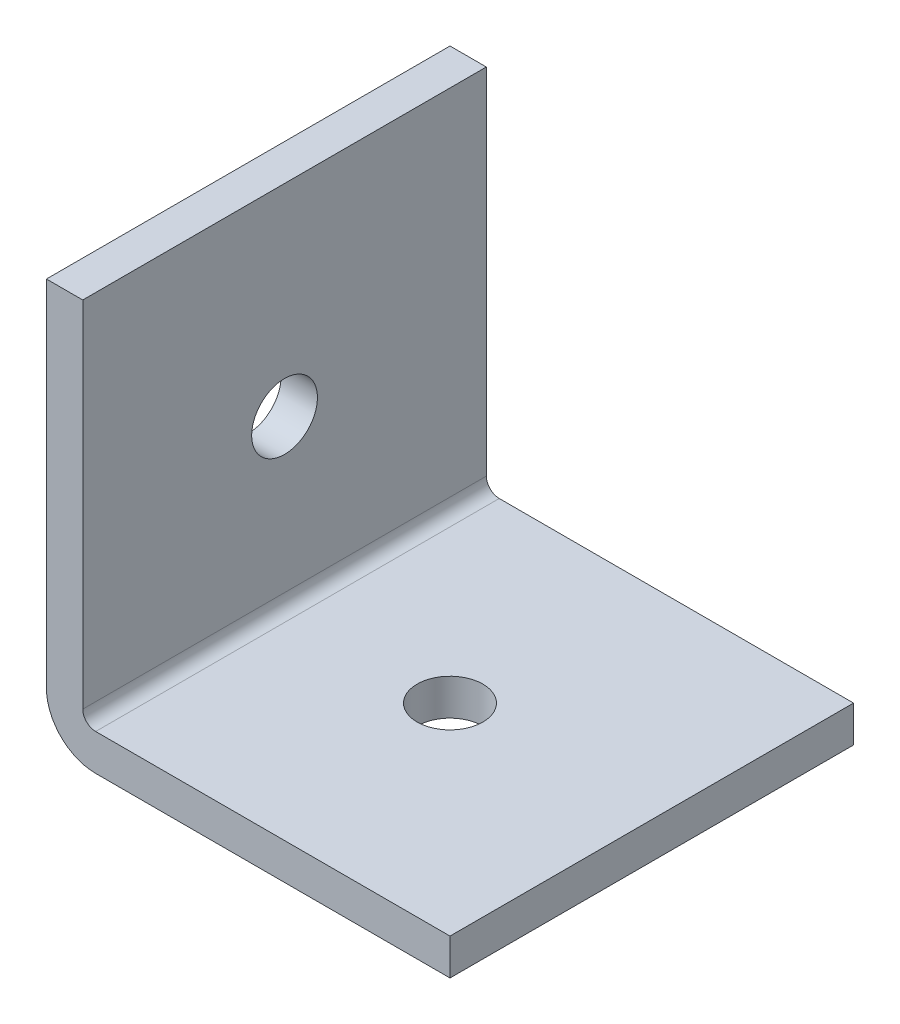
SolidWorks part; units mm, degrees
material "6061-T6 (SS)"
ref_plane "Front Plane" through (0, 0, 0) normal (0, 0, 1) x (1, 0, 0)
ref_plane "Top Plane" through (0, 0, 0) normal (0, 1, 0) x (1, 0, 0)
ref_plane "Right Plane" through (0, 0, 0) normal (1, 0, 0) x (0, 0, -1)
ref_plane "Plane1" through (0, 0, 0) normal (-1, 0, 0) x (0, -1, 0)
sketch "Sketch1" plane through (0, 0, 0) normal (-1, 0, 0) x (0, -1, 0)
  line L0 (0, 749.3) -> (-25.4, 749.3)
  line L1 (-25.4, 749.3) -> (-25.4, -749.3)
  line L2 (-25.4, -749.3) -> (0, -749.3)
  line L3 (0, -749.3) -> (0, 749.3)
extrude "Boss-Extrude1" add sketch "Sketch1" against normal blind 25.4
sketch "Sketch2" plane through (0, 0, -749.3) normal (0, 0, -1) x (-1, 0, 0)
  line L0 (-25.4, 2.286) -> (-2.286, 2.286)
  line L1 (-2.286, 2.286) -> (-2.286, 25.4)
  line L2 (-2.286, 25.4) -> (-25.4, 25.4)
  line L3 (-25.4, 25.4) -> (-25.4, 2.286)
extrude "Cut-Extrude1" cut sketch "Sketch2" against normal through all
hole_wizard "M3.5 Clearance Hole1" positions "Sketch4" profile "Sketch3" hole size "M3.5" standard "ANSI Metric"
sketch "Sketch4" plane through (0, 0, 0) normal (0, -1, 0) x (-1, 0, 0)
  point P0 (-12.7, 736.6)
  point P1 (-12.7, 711.2)
  point P2 (-12.7, 685.8)
  point P3 (-12.7, 660.4)
  point P4 (-12.7, 635)
  point P5 (-12.7, 609.6)
  point P6 (-12.7, 584.2)
  point P7 (-12.7, 558.8)
  point P8 (-12.7, 533.4)
  point P9 (-12.7, 508)
  point P10 (-12.7, 482.6)
  point P11 (-12.7, 457.2)
  point P12 (-12.7, 431.8)
  point P13 (-12.7, 406.4)
  point P14 (-12.7, 381)
  point P15 (-12.7, 355.6)
  point P16 (-12.7, 330.2)
  point P17 (-12.7, 304.8)
  point P18 (-12.7, 279.4)
  point P19 (-12.7, 254)
  point P20 (-12.7, 228.6)
  point P21 (-12.7, 203.2)
  point P22 (-12.7, 177.8)
  point P23 (-12.7, 152.4)
  point P24 (-12.7, 127)
  point P25 (-12.7, 101.6)
  point P26 (-12.7, 76.2)
  point P27 (-12.7, 50.8)
  point P28 (-12.7, 25.4)
  point P29 (-12.7, 0)
  point P30 (-12.7, -25.4)
  point P31 (-12.7, -50.8)
  point P32 (-12.7, -76.2)
  point P33 (-12.7, -101.6)
  point P34 (-12.7, -127)
  point P35 (-12.7, -152.4)
  point P36 (-12.7, -177.8)
  point P37 (-12.7, -203.2)
  point P38 (-12.7, -228.6)
  point P39 (-12.7, -254)
  point P40 (-12.7, -279.4)
  point P41 (-12.7, -304.8)
  point P42 (-12.7, -330.2)
  point P43 (-12.7, -355.6)
  point P44 (-12.7, -381)
  point P45 (-12.7, -406.4)
  point P46 (-12.7, -431.8)
  point P47 (-12.7, -457.2)
  point P48 (-12.7, -482.6)
  point P49 (-12.7, -508)
  point P50 (-12.7, -533.4)
  point P51 (-12.7, -558.8)
  point P52 (-12.7, -584.2)
  point P53 (-12.7, -609.6)
  point P54 (-12.7, -635)
  point P55 (-12.7, -660.4)
  point P56 (-12.7, -685.8)
  point P57 (-12.7, -711.2)
  point P58 (-12.7, -736.6)
sketch "Sketch3" plane through (12.7, 0, -736.6) normal (1, 0, 0) x (0, 0, -1)
  line L0 (0, 0) -> (0, 25.4)
  line L1 (0, 25.4) -> (2.0701, 25.4)
  line L2 (2.0701, 25.4) -> (2.0701, 0)
  line L5 (2.0701, 0) -> (0, 0)
  line L11 (0, -6.35) -> (0, 107.95) construction
  dimension "Thru Hole Dia." = 4.1402
  dimension "Thru Hole Depth" = 25.4
hole_wizard "M3.5 Clearance Hole2" positions "Sketch6" profile "Sketch5" hole size "M3.5" standard "ANSI Metric"
sketch "Sketch6" plane through (0, 0, 0) normal (-1, 0, 0) x (0, 0, 1)
  point P0 (711.2, 12.7)
  point P1 (736.6, 12.7)
  point P2 (685.8, 12.7)
  point P3 (660.4, 12.7)
  point P4 (635, 12.7)
  point P5 (609.6, 12.7)
  point P6 (584.2, 12.7)
  point P7 (558.8, 12.7)
  point P8 (533.4, 12.7)
  point P9 (508, 12.7)
  point P10 (482.6, 12.7)
  point P11 (457.2, 12.7)
  point P12 (431.8, 12.7)
  point P13 (406.4, 12.7)
  point P14 (381, 12.7)
  point P15 (355.6, 12.7)
  point P16 (330.2, 12.7)
  point P17 (304.8, 12.7)
  point P18 (279.4, 12.7)
  point P19 (254, 12.7)
  point P20 (228.6, 12.7)
  point P21 (203.2, 12.7)
  point P22 (177.8, 12.7)
  point P23 (152.4, 12.7)
  point P24 (127, 12.7)
  point P25 (101.6, 12.7)
  point P26 (76.2, 12.7)
  point P27 (50.8, 12.7)
  point P28 (25.4, 12.7)
  point P29 (0, 12.7)
  point P30 (-25.4, 12.7)
  point P31 (-50.8, 12.7)
  point P32 (-76.2, 12.7)
  point P33 (-101.6, 12.7)
  point P34 (-127, 12.7)
  point P35 (-152.4, 12.7)
  point P36 (-177.8, 12.7)
  point P37 (-203.2, 12.7)
  point P38 (-228.6, 12.7)
  point P39 (-254, 12.7)
  point P40 (-279.4, 12.7)
  point P41 (-304.8, 12.7)
  point P42 (-330.2, 12.7)
  point P43 (-355.6, 12.7)
  point P44 (-381, 12.7)
  point P45 (-406.4, 12.7)
  point P46 (-431.8, 12.7)
  point P47 (-457.2, 12.7)
  point P48 (-482.6, 12.7)
  point P49 (-508, 12.7)
  point P50 (-533.4, 12.7)
  point P51 (-558.8, 12.7)
  point P52 (-584.2, 12.7)
  point P53 (-609.6, 12.7)
  point P54 (-635, 12.7)
  point P55 (-660.4, 12.7)
  point P56 (-685.8, 12.7)
  point P57 (-711.2, 12.7)
  point P58 (-736.6, 12.7)
sketch "Sketch5" plane through (0, 12.7, 711.2) normal (0, 1, 0) x (0, 0, 1)
  line L0 (0, 0) -> (0, 25.4)
  line L1 (0, 25.4) -> (2.0701, 25.4)
  line L2 (2.0701, 25.4) -> (2.0701, 0)
  line L5 (2.0701, 0) -> (0, 0)
  line L11 (0, -6.35) -> (0, 107.95) construction
  dimension "Thru Hole Dia." = 4.1402
  dimension "Thru Hole Depth" = 25.4
chamfer "Chamfer1" distance 2.159 angle 45 4 edges at (25.4, 1.143, -749.3) (1.143, 25.4, -749.3) (1.143, 25.4, 749.3) (25.4, 1.143, 749.3)
fillet "Fillet1" radius 0.8128 1 edges at (2.286, 2.286, 0)
fillet "Fillet2" radius 3.0988 1 edges at (0, 0, 0)
sketch "Sketch8" plane through (0, 0, 749.3) normal (0, 0, 1) x (1, 0, 0)
  line L1 (-45.6555, -36.5704) -> (50.2275, -36.5704)
  line L2 (-45.6555, -36.5704) -> (-45.6555, 42.768)
  line L3 (-45.6555, 42.768) -> (50.2275, 42.768)
  line L4 (50.2275, -36.5704) -> (50.2275, 42.768)
  line L5 (-45.6555, -36.5704) -> (50.2275, 42.768) construction
  line L6 (-45.6555, 42.768) -> (50.2275, -36.5704) construction
  point P0 (2.286, 3.0988)
extrude "Cut-Extrude3" cut sketch "Sketch8" against normal blind 1371.6
sketch "Sketch9" plane through (0, 0, -749.3) normal (0, 0, -1) x (-1, 0, 0)
  line L1 (26.2815, -24.3339) -> (-30.643, -24.3339)
  line L2 (26.2815, -24.3339) -> (26.2815, 26.9489)
  line L3 (26.2815, 26.9489) -> (-30.643, 26.9489)
  line L4 (-30.643, -24.3339) -> (-30.643, 26.9489)
  line L5 (26.2815, -24.3339) -> (-30.643, 26.9489) construction
  line L6 (26.2815, 26.9489) -> (-30.643, -24.3339) construction
  point P0 (-2.1808, 1.3075)
extrude "Cut-Extrude4" cut sketch "Sketch9" against normal blind 76.2
sketch "Sketch10" plane through (0, 0, -622.3) normal (0, 0, 1) x (1, 0, 0)
  line L1 (-26.4819, -25.6422) -> (30.7654, -25.6422)
  line L2 (-26.4819, -25.6422) -> (-26.4819, 28.0701)
  line L3 (-26.4819, 28.0701) -> (30.7654, 28.0701)
  line L4 (30.7654, -25.6422) -> (30.7654, 28.0701)
  line L5 (-26.4819, -25.6422) -> (30.7654, 28.0701) construction
  line L6 (-26.4819, 28.0701) -> (30.7654, -25.6422) construction
  point P0 (2.1417, 1.2139)
extrude "Cut-Extrude5" cut sketch "Sketch10" against normal blind 25.4
